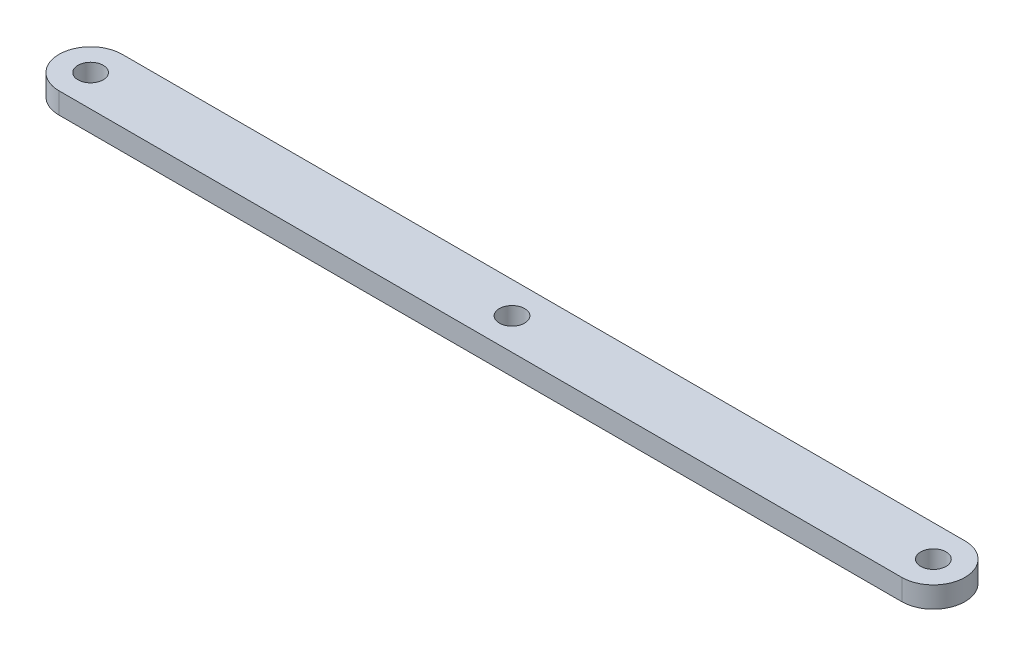
SolidWorks part; units mm, degrees
ref_plane "Front Plane" through (0, 0, 0) normal (0, 0, 1) x (1, 0, 0)
ref_plane "Top Plane" through (0, 0, 0) normal (0, 1, 0) x (1, 0, 0)
ref_plane "Right Plane" through (0, 0, 0) normal (1, 0, 0) x (0, 0, -1)
sketch "Sketch1" plane through (0, 0, 0) normal (0, 1, 0) x (1, 0, 0)
  line L0 (0, 7.5) -> (200, 7.5)
  line L1 (0, -7.5) -> (200, -7.5)
  arc A0 (0, 7.5) -> (0, -7.5) centre (0, 0) ccw
  arc A1 (200, -7.5) -> (200, 7.5) centre (200, 0) ccw
  circle A2 centre (200, 0) radius 3
  circle A3 centre (0, 0) radius 3
  circle A4 centre (100, 0) radius 3
  dimension "D1" = 15
  dimension "D3" = 6
  dimension "D4" = 6
  dimension "D5" = 6
  dimension "D2" = 200
  dimension "D6" = 100
extrude "Boss-Extrude1" add sketch "Sketch1" along normal blind 5
